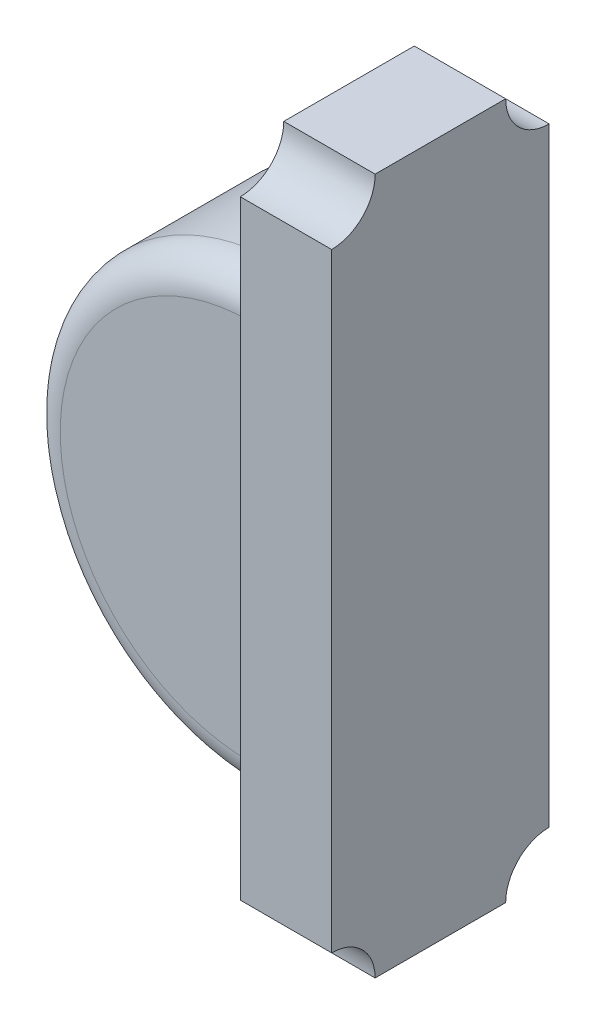
SolidWorks part; units mm, degrees
ref_plane "Płaszczyzna przednia" through (0, 0, 0) normal (0, 0, 1) x (1, 0, 0)
ref_plane "Płaszczyzna górna" through (0, 0, 0) normal (0, 1, 0) x (1, 0, 0)
ref_plane "Płaszczyzna prawa" through (0, 0, 0) normal (1, 0, 0) x (0, 0, -1)
ref_plane "Płaszczyzna1" through (-41.05, 0, 0) normal (1, 0, 0) x (0, 0, -1)
sketch "Szkic1" plane through (-41.05, 0, 0) normal (1, 0, 0) x (0, 0, -1)
  line L0 (-2.4, -13.4) -> (-1.8, -13.4)
  line L1 (-1.6, -13.6) -> (-1.6, -16.4)
  line L2 (-2.4, -16.6) -> (-1.8, -16.6)
  line L3 (-2.6, -16.4) -> (-2.6, -13.6)
  arc A0 (-2.6, -13.6) -> (-2.4, -13.4) centre (-2.6, -13.4) ccw
  arc A1 (-1.8, -13.4) -> (-1.6, -13.6) centre (-1.6, -13.4) ccw
  arc A2 (-2.6, -16.4) -> (-2.4, -16.6) centre (-2.6, -16.6) cw
  arc A3 (-1.6, -16.4) -> (-1.8, -16.6) centre (-1.6, -16.6) ccw
extrude "Dodanie-wyciągnięcie1" add sketch "Szkic1" against normal blind 0.42
sketch "Szkic2" plane through (0, 0, 2.6) normal (0, 0, 1) x (1, 0, 0)
  line L0 (-41.47, -13.6) -> (-41.47, -16.4) construction
  line L1 (-41.47, -13.9726) -> (-41.47, -16.0274)
  arc A0 (-41.47, -13.9726) -> (-41.47, -16.0274) centre (-41.47, -15) ccw
extrude "Dodanie-wyciągnięcie2" add sketch "Szkic2" against normal blind 0.9 from offset 0.05 separate body offset against normal yes
fillet "Zaokrąglenie1" radius 0.15 2 edges at (-42.4974, -15, 1.65) (-42.4974, -15, 2.55)
